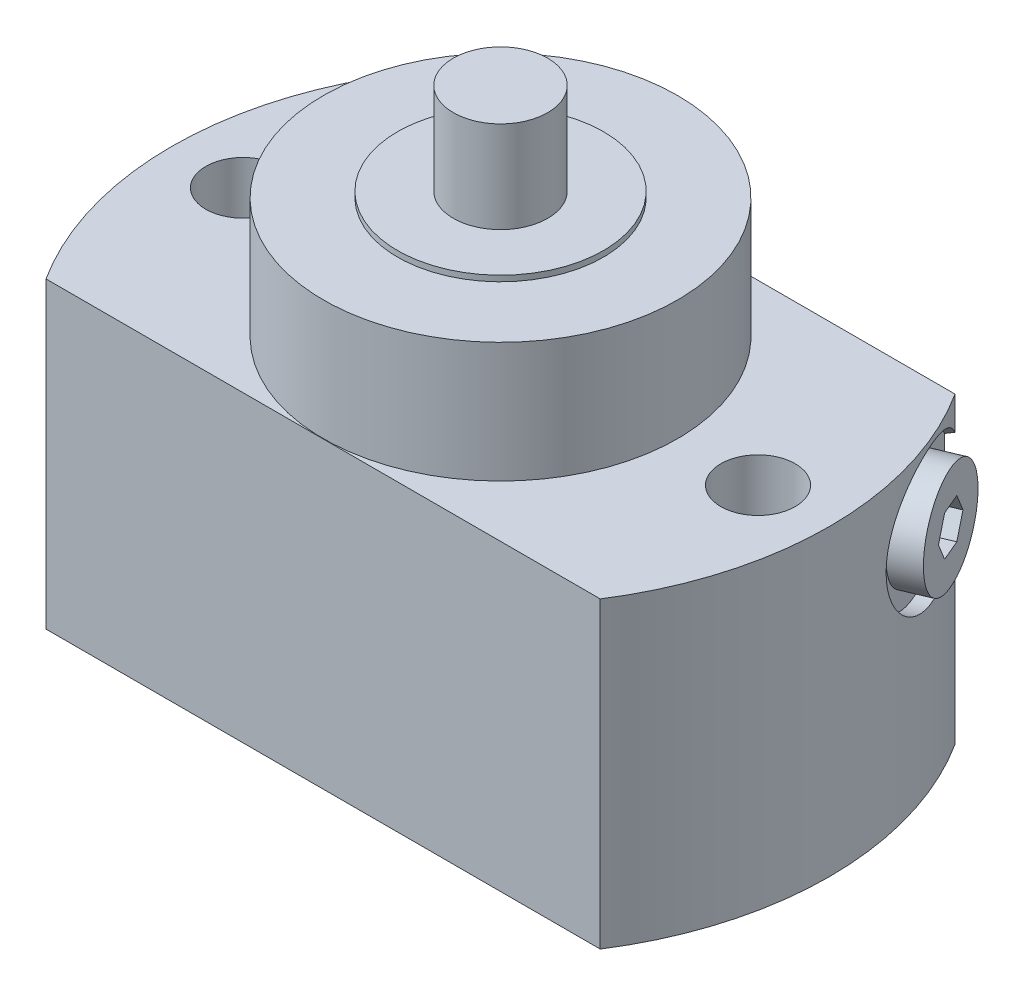
SolidWorks part; units mm, degrees
material "Alloy Steel"
ref_plane "Front Plane" through (0, 0, 0) normal (0, 0, 1) x (1, 0, 0)
ref_plane "Top Plane" through (0, 0, 0) normal (0, 1, 0) x (1, 0, 0)
ref_plane "Right Plane" through (0, 0, 0) normal (1, 0, 0) x (0, 0, -1)
sketch "Sketch1" plane through (0, 0, 0) normal (0, 1, 0) x (1, 0, 0)
  line L0 (-48.4278, 31) -> (48.4278, 31)
  line L1 (0, 0) -> (70.7148, 0) construction
  line L2 (-48.4278, -31) -> (48.4278, -31)
  arc A0 (-48.4278, 31) -> (-48.4278, -31) centre (0, 0) ccw
  arc A1 (48.4278, -31) -> (48.4278, 31) centre (0, 0) ccw
  dimension "D1" = 57.5
  dimension "D2" = 62
extrude "Extrude1" add sketch "Sketch1" along normal blind 53
sketch "Sketch2" plane through (0, 0, 0) normal (0, 0, 1) x (1, 0, 0)
  line L0 (0, 0) -> (0, 90.1953) construction
  line L1 (0, 91) -> (-8.25, 91)
  line L2 (-8.25, 91) -> (-8.25, 75)
  line L3 (-8.25, 75) -> (-18, 75)
  line L4 (-18, 75) -> (-18, 74)
  line L5 (-18, 74) -> (-30.95, 74)
  line L6 (-30.95, 74) -> (-30.95, 53)
  line L7 (-48.4278, 53) -> (48.4278, 53) construction
  line L8 (-30.95, 53) -> (0, 53)
  line L9 (0, 53) -> (0, 91)
  line L10 (-48.4278, 0) -> (48.4278, 0) construction
  dimension "D1" = 16.5
  dimension "D2" = 16
  dimension "D3" = 75
  dimension "D4" = 1
  dimension "D5" = 36
  dimension "D6" = 61.9
revolve "Revolve1" add sketch "Sketch2" angle 360 about L0
hole_wizard "Hole1" positions "Sketch4" profile "Sketch3" legacy end condition up to next
sketch "Sketch4" plane through (0, 53, 0) normal (0, 1, 0) x (-1, 0, 0)
  line L0 (0, 0) -> (0, 47.5777) construction
  point P0 (45, 0)
  point P7 (-45, 0)
  dimension "D1" = 90
sketch "Sketch3" plane through (-45, 53, 0) normal (1, 0, 0) x (0, 0, 1)
  line L0 (0, 0) -> (0, 53)
  line L1 (0, 53) -> (6.5, 53)
  line L2 (6.5, 53) -> (6.5, 0)
  line L3 (6.5, 0) -> (0, 0)
  line L4 (0, 110) -> (0, -10) construction
  dimension "Diameter" = 13
  dimension "Depth" = 53
sketch "Sketch5" plane through (0, 0, 0) normal (0, -1, 0) x (1, 0, 0)
  circle A0 centre (0, 0) radius 4
  dimension "D1" = 8
extrude "Cut-Extrude1" cut sketch "Sketch5" against normal blind 4
sketch "Sketch6" plane through (0, 0, 0) normal (0, -1, 0) x (1, 0, 0)
  circle A0 centre (35, -15) radius 5.5
  dimension "D3" = 11
  dimension "D1" = 35
  dimension "D2" = 15
extrude "Cut-Extrude2" cut sketch "Sketch6" against normal blind 3
sketch "Sketch7" plane through (0, 3, 0) normal (0, -1, 0) x (1, 0, 0)
  circle A0 centre (35, -15) radius 2
  dimension "D1" = 4
extrude "Cut-Extrude3" cut sketch "Sketch7" against normal blind 33
ref_plane "Plane1" through (0, 0, 0) normal (0.3907, 0, 0.9205) x (0.9205, 0, -0.3907)
sketch "Sketch8" plane through (0, 0, 0) normal (0.3907, 0, 0.9205) x (0.9205, 0, -0.3907)
  line L0 (51.5856, 40) -> (-19.0781, 40) construction
  line L1 (-56.6907, 0) -> (32.4653, 0) construction
  line L2 (57.5, 28) -> (55, 28)
  line L3 (57.5, 0) -> (57.5, 53) construction
  line L4 (55, 28) -> (55, 33.4215)
  line L5 (55, 33.4215) -> (53.5174, 34.2775)
  line L6 (53.5174, 34.2775) -> (35, 34.2775)
  line L7 (35, 34.2775) -> (35, 40)
  line L8 (35, 40) -> (57.5, 40)
  line L9 (57.5, 40) -> (57.5, 28)
  dimension "D1" = 40
  dimension "D2" = 2.5
  dimension "D3" = 20
  dimension "D4" = 11.445
  dimension "D5" = 24
  dimension "D6" = 30
  dimension "D7" = 13.157
revolve "Cut-Revolve1" cut sketch "Sketch8" angle 360 about L0
sketch "Sketch9" plane through (0, 0, 0) normal (0.3907, 0, 0.9205) x (0.9205, 0, -0.3907)
  line L0 (74.5879, 40) -> (15.4121, 40) construction
  line L1 (35, 40) -> (53.5174, 40) construction
  line L2 (55, 28) -> (55, 52) construction
  line L4 (55, 31) -> (55, 34.2775)
  line L5 (46, 34.2775) -> (55, 34.2775)
  line L6 (55, 31) -> (60, 31)
  line L7 (60, 31) -> (60, 40)
  line L8 (60, 40) -> (45, 40)
  line L9 (45, 40) -> (45, 35.2775)
  line L10 (45, 35.2775) -> (46, 34.2775)
  line L12 (40.0743, 34.2775) -> (53.5174, 34.2775) construction
  dimension "D1" = 45
  dimension "D2" = 4.7225
  dimension "D3" = 10
  dimension "D4" = 5
  dimension "D5" = 18
revolve "Revolve2" add sketch "Sketch9" angle 360 about L0
sketch "Sketch10" plane through (55.2303, 0, -23.4439) normal (0.9205, 0, -0.3907) x (-0.3907, 0, -0.9205)
  line L1 (4.0415, 40) -> (2.0207, 43.5)
  line L2 (2.0207, 43.5) -> (-2.0207, 43.5)
  line L3 (-2.0207, 43.5) -> (-4.0415, 40)
  line L4 (-4.0415, 40) -> (-2.0207, 36.5)
  line L5 (-2.0207, 36.5) -> (2.0207, 36.5)
  line L6 (2.0207, 36.5) -> (4.0415, 40)
  circle A0 centre (0, 40) radius 3.5 construction
  circle A1 centre (0, 40) radius 9 construction
  dimension "D1" = 7
extrude "Cut-Extrude4" cut sketch "Sketch10" against normal blind 5
